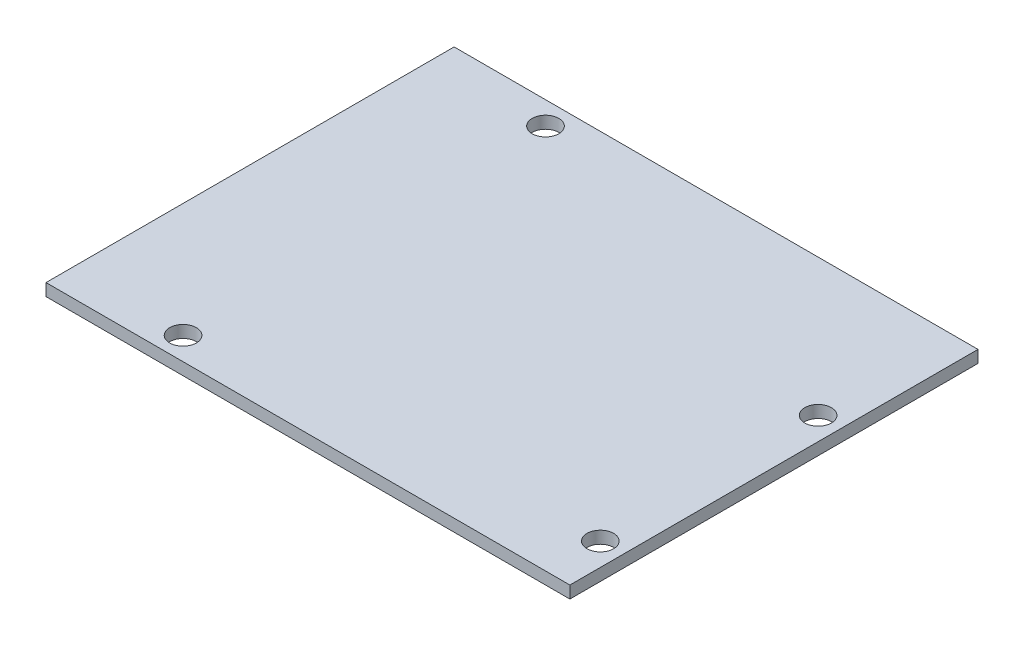
SolidWorks part; units mm, degrees
ref_plane "Front Plane" through (0, 0, 0) normal (0, 0, 1) x (1, 0, 0)
ref_plane "Top Plane" through (0, 0, 0) normal (0, 1, 0) x (1, 0, 0)
ref_plane "Right Plane" through (0, 0, 0) normal (1, 0, 0) x (0, 0, -1)
sketch "Sketch1" plane through (0, 0, 0) normal (0, 1, 0) x (-1, 0, 0)
  line L1 (-34.4, 26.8) -> (34.4, 26.8)
  line L2 (-34.4, 26.8) -> (-34.4, -26.8)
  line L3 (-34.4, -26.8) -> (34.4, -26.8)
  line L4 (34.4, 26.8) -> (34.4, -26.8)
  line L5 (-34.4, 26.8) -> (34.4, -26.8) construction
  line L6 (-34.4, -26.8) -> (34.4, 26.8) construction
  point P0 (0, 0)
  dimension "D1" = 53.6
  dimension "D2" = 68.8
extrude "Boss-Extrude1" add sketch "Sketch1" along normal blind 1.6
sketch "Sketch2" plane through (0, 1.6, 0) normal (0, 1, 0) x (-1, 0, 0)
  line L0 (34.4, -26.8) -> (34.4, 26.8) construction
  line L1 (-34.4, -26.8) -> (34.4, -26.8) construction
  line L2 (34.4, 26.8) -> (-34.4, 26.8) construction
  line L3 (-34.4, 26.8) -> (-34.4, -26.8) construction
  circle A0 centre (19.4, -23.8) radius 1.75
  circle A1 centre (19.4, 23.8) radius 1.75
  circle A2 centre (-31.4, 19.8) radius 1.75
  circle A3 centre (-31.4, -8.8) radius 1.75
  dimension "D1" = 3.5
  dimension "D2" = 3.5
  dimension "D3" = 3.5
  dimension "D4" = 3.5
  dimension "D5" = 15
  dimension "D6" = 3
  dimension "D7" = 15
  dimension "D8" = 3
  dimension "D9" = 3
  dimension "D10" = 18
  dimension "D11" = 3
  dimension "D12" = 7
extrude "Cut-Extrude1" cut sketch "Sketch2" against normal up to next
